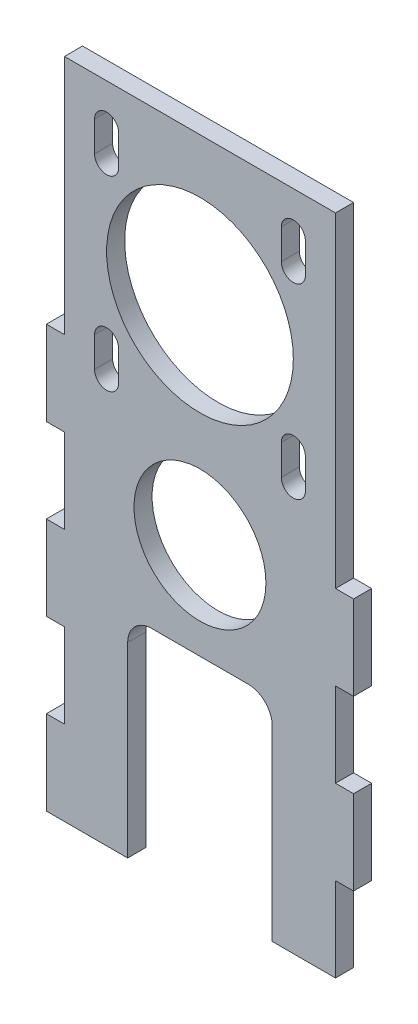
SolidWorks part; units mm, degrees
material "PC High Viscosity"
ref_plane "Front Plane" through (0, 0, 0) normal (0, 0, 1) x (1, 0, 0)
ref_plane "Top Plane" through (0, 0, 0) normal (0, 1, 0) x (1, 0, 0)
ref_plane "Right Plane" through (0, 0, 0) normal (1, 0, 0) x (0, 0, -1)
sketch "Sketch1" plane through (0, 0, 0) normal (0, 0, 1) x (1, 0, 0)
  line L1 (-22.5, -55) -> (22.5, -55)
  line L2 (-22.5, -55) -> (-22.5, 55)
  line L3 (-22.5, 55) -> (22.5, 55)
  line L4 (22.5, -55) -> (22.5, 55)
  line L5 (-22.5, -55) -> (22.5, 55) construction
  line L6 (-22.5, 55) -> (22.5, -55) construction
  point P0 (0, 0)
  dimension "D1" = 110
  dimension "D2" = 45
extrude "Boss-Extrude1" add sketch "Sketch1" along normal blind 3
sketch "Sketch2" plane through (0, 0, 3) normal (0, 0, 1) x (1, 0, 0)
  line L0 (-22.5, -55) -> (22.5, -55) construction
  line L1 (-12, -20) -> (12, -20)
  line L2 (-12, -20) -> (-12, -55)
  line L3 (-12, -55) -> (12, -55)
  line L4 (12, -20) -> (12, -55)
  line L5 (-12, -20) -> (12, -55) construction
  line L6 (-12, -55) -> (12, -20) construction
  line L7 (-22.5, 55) -> (-22.5, -55) construction
  line L8 (-22.5, 15) -> (22.5, 15) construction
  line L9 (-22.5, 15) -> (-22.5, -55) construction
  line L10 (-22.5, -55) -> (22.5, -55) construction
  line L11 (22.5, 15) -> (22.5, -55) construction
  line L12 (-22.5, 15) -> (22.5, -55) construction
  line L13 (-22.5, -55) -> (22.5, 15) construction
  line L14 (-15.5, 43.5) -> (-15.5, 48.5) construction
  line L15 (-15.5, 15) -> (15.5, 15) construction
  line L16 (-15.5, 15) -> (-15.5, 46) construction
  line L17 (-15.5, 46) -> (15.5, 46) construction
  line L18 (15.5, 15) -> (15.5, 46) construction
  line L19 (-15.5, 15) -> (15.5, 46) construction
  line L20 (-15.5, 46) -> (15.5, 15) construction
  line L21 (-17.5, 43.5) -> (-17.5, 48.5)
  line L22 (-13.5, 43.5) -> (-13.5, 48.5)
  line L23 (-15.5, 17.5) -> (-15.5, 12.5) construction
  line L24 (-13.5, 17.5) -> (-13.5, 12.5)
  line L25 (-17.5, 17.5) -> (-17.5, 12.5)
  line L26 (15.5, 17.5) -> (15.5, 12.5) construction
  line L27 (17.5, 17.5) -> (17.5, 12.5)
  line L28 (13.5, 17.5) -> (13.5, 12.5)
  line L29 (15.5, 43.5) -> (15.5, 48.5) construction
  line L30 (13.5, 43.5) -> (13.5, 48.5)
  line L31 (17.5, 43.5) -> (17.5, 48.5)
  circle A0 centre (0, -4) radius 10.95
  arc A1 (-17.5, 43.5) -> (-13.5, 43.5) centre (-15.5, 43.5) ccw
  arc A2 (-13.5, 48.5) -> (-17.5, 48.5) centre (-15.5, 48.5) ccw
  arc A3 (-13.5, 17.5) -> (-17.5, 17.5) centre (-15.5, 17.5) ccw
  arc A4 (-17.5, 12.5) -> (-13.5, 12.5) centre (-15.5, 12.5) ccw
  circle A5 centre (0, 30.5) radius 15.5
  arc A6 (17.5, 17.5) -> (13.5, 17.5) centre (15.5, 17.5) ccw
  arc A7 (13.5, 12.5) -> (17.5, 12.5) centre (15.5, 12.5) ccw
  arc A8 (13.5, 43.5) -> (17.5, 43.5) centre (15.5, 43.5) ccw
  arc A9 (17.5, 48.5) -> (13.5, 48.5) centre (15.5, 48.5) ccw
  point P0 (0, -37.5)
  point P7 (0, -20)
  point P17 (0, 30.5)
  point P24 (-15.5, 46)
  point P33 (-15.5, 15)
  point P38 (15.5, 15)
  point P43 (15.5, 46)
  dimension "D4" = 21.9
  dimension "D7" = 2
  dimension "D1" = 35
  dimension "D2" = 70
  dimension "D3" = 24
  dimension "D5" = 16
  dimension "D6" = 31
  dimension "D8" = 5
extrude "Cut-Extrude1" cut sketch "Sketch2" against normal through all
fillet "Fillet1" radius 4 2 edges at (12, -20, 1.5) (-12, -20, 1.5)
sketch "Sketch3" plane through (0, 0, 3) normal (0, 0, 1) x (1, 0, 0)
  line L0 (22.5, -55) -> (22.5, 55) construction
  line L1 (-22.5, -55) -> (22.5, -55) construction
  line L2 (-22.5, -55) -> (-22.5, 15) construction
  line L3 (-22.5, 15) -> (22.5, 15) construction
  line L4 (22.5, -55) -> (22.5, 15) construction
  line L5 (-22.5, -13) -> (-22.5, -27)
  line L6 (-22.5, 15) -> (-25.5, 15)
  line L7 (-22.5, 15) -> (-22.5, 1)
  line L8 (-22.5, 1) -> (-25.5, 1)
  line L9 (-25.5, 15) -> (-25.5, 1)
  line L10 (-22.5, -27) -> (-25.5, -27)
  line L11 (-25.5, -13) -> (-25.5, -27)
  line L12 (-22.5, -13) -> (-25.5, -13)
  line L13 (-22.5, -41) -> (-22.5, -55)
  line L14 (-22.5, -55) -> (-25.5, -55)
  line L15 (-25.5, -41) -> (-25.5, -55)
  line L16 (-22.5, -41) -> (-25.5, -41)
  line L18 (-22.5, 55) -> (-22.5, -55) construction
  line L20 (22.5, 1) -> (25.5, 1)
  line L21 (22.5, 1) -> (22.5, -13)
  line L22 (22.5, -13) -> (25.5, -13)
  line L23 (25.5, 1) -> (25.5, -13)
  line L24 (22.5, -27) -> (25.5, -27)
  line L25 (22.5, -27) -> (22.5, -41)
  line L26 (22.5, -41) -> (25.5, -41)
  line L27 (25.5, -27) -> (25.5, -41)
  dimension "D1" = 70
  dimension "D2" = 3
  dimension "D3" = 14
  dimension "D4" = 3
extrude "Boss-Extrude2" add sketch "Sketch3" against normal up to surface (3 mm away) up to face at (15.5, 46, 0)
equation "\"pulley_pitch_diam\"= 12.73mm"
equation "\"pulley_total_width\"= 16mm"
equation "\"pulley_total_diam\"= 16mm"
equation "\"belt_width\"= 6mm"
equation "\"material_thickness\"= 3mm"
equation "\"shaft_diam\"= 8mm"
equation "\"bearing_od\"= 22mm"
equation "\"bearing_thickness\"= 7mm"
equation "\"D1@Boss-Extrude1\"=\"material_thickness\""
equation "\"D3@Sketch2\"=\"pulley_total_width\" * 1.5"
equation "\"D4@Sketch2\"=\"bearing_od\" - 0.1"
equation "\"D2@Sketch3\"=\"material_thickness\""
equation "\"D5@Sketch2\"=\"pulley_total_diam\""
